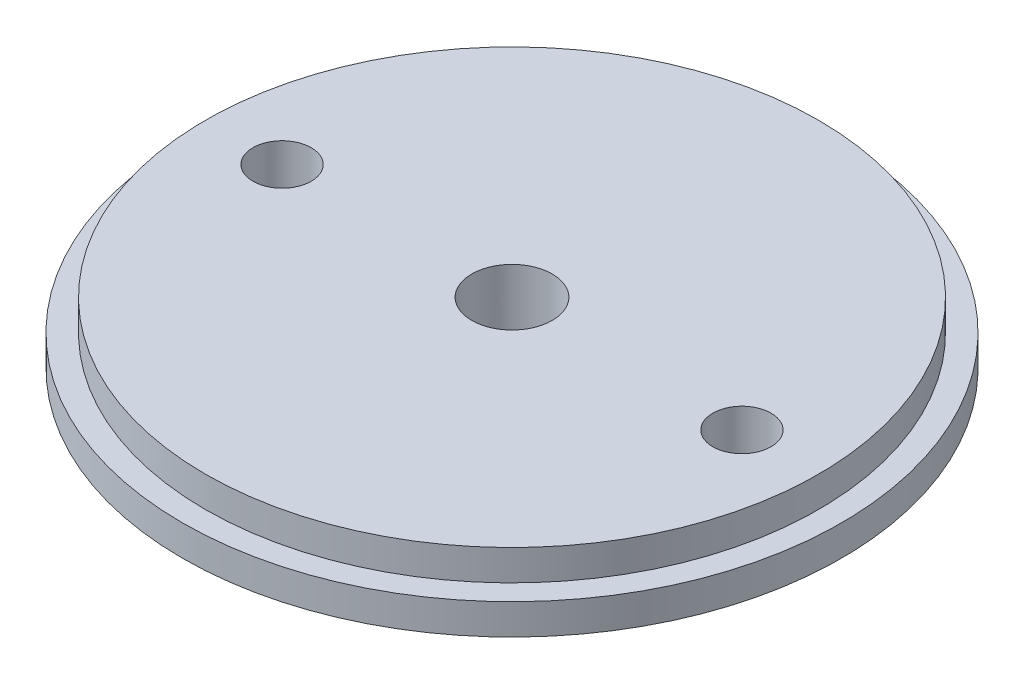
SolidWorks part; units mm, degrees
material "A-Glass Fiber"
ref_plane "Front Plane" through (0, 0, 0) normal (0, 0, 1) x (1, 0, 0)
ref_plane "Top Plane" through (0, 0, 0) normal (0, 1, 0) x (1, 0, 0)
ref_plane "Right Plane" through (0, 0, 0) normal (1, 0, 0) x (0, 0, -1)
sketch "Sketch1" plane through (0, 0, 0) normal (0, 1, 0) x (1, 0, 0)
  circle A0 centre (0, 0) radius 27.305
  dimension "D1" = 54.61
extrude "Boss-Extrude1" add sketch "Sketch1" along normal blind 2.54
sketch "Sketch2" plane through (0, 2.54, 0) normal (0, 1, 0) x (1, 0, 0)
  circle A0 centre (0, 0) radius 25.4
  dimension "D1" = 50.8
extrude "Boss-Extrude2" add sketch "Sketch2" along normal blind 2.54
sketch "Sketch3" plane through (0, 0, 0) normal (0, -1, 0) x (1, 0, 0)
  circle A0 centre (0, 0) radius 3.3346
  circle A1 centre (-19.05, 0) radius 2.413
  circle A2 centre (19.05, 0) radius 2.413
  dimension "D1" = 4.826
  dimension "D2" = 19.05
  dimension "D3" = 19.05
extrude "Cut-Extrude1" cut sketch "Sketch3" against normal up to next
